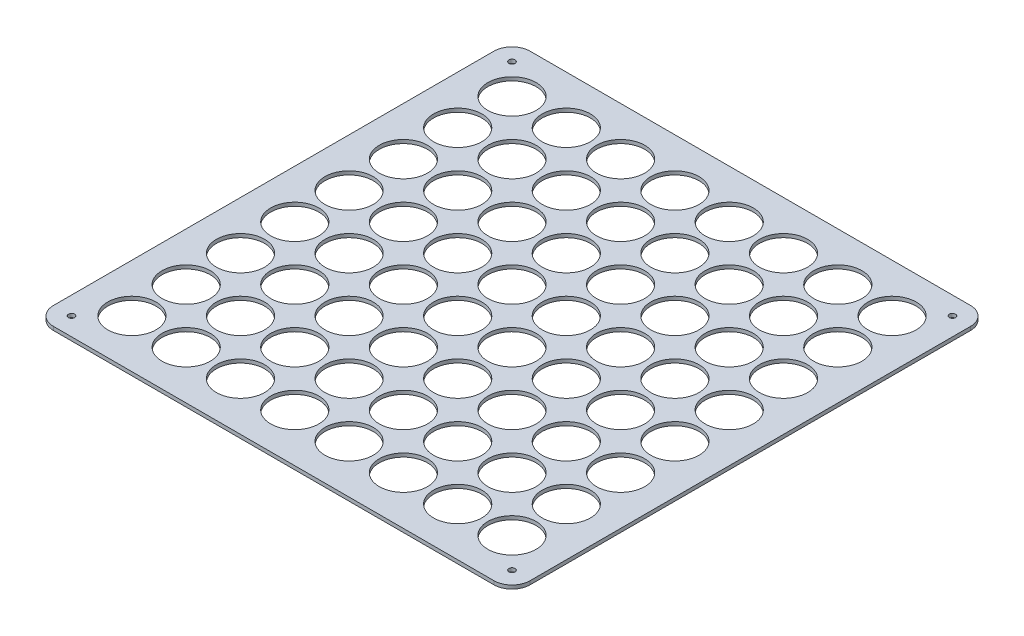
SolidWorks part; units mm, degrees
ref_plane "Front Plane" through (0, 0, 0) normal (0, 0, 1) x (1, 0, 0)
ref_plane "Top Plane" through (0, 0, 0) normal (0, 1, 0) x (1, 0, 0)
ref_plane "Right Plane" through (0, 0, 0) normal (1, 0, 0) x (0, 0, -1)
sketch "Sketch1" plane through (0, 0, 0) normal (0, 1, 0) x (1, 0, 0)
  line L1 (-197.5, 197.5) -> (197.5, 197.5)
  line L2 (-197.5, 197.5) -> (-197.5, -197.5)
  line L3 (-197.5, -197.5) -> (197.5, -197.5)
  line L4 (197.5, 197.5) -> (197.5, -197.5)
  line L5 (-197.5, 197.5) -> (197.5, -197.5) construction
  line L6 (-197.5, -197.5) -> (197.5, 197.5) construction
  circle A0 centre (-182.5, 182.5) radius 2.55
  circle A1 centre (182.5, 182.5) radius 2.55
  circle A2 centre (182.5, -182.5) radius 2.55
  circle A3 centre (-182.5, -182.5) radius 2.55
  point P0 (0, 0)
  dimension "D4" = 5.1
  dimension "D6" = 5.1
  dimension "D8" = 5.1
  dimension "D10" = 5.1
  dimension "D1" = 395
  dimension "D2" = 395
  dimension "D3" = 15
  dimension "D5" = 15
  dimension "D7" = 15
  dimension "D9" = 15
extrude "Boss-Extrude1" add sketch "Sketch1" along normal blind 3
fillet "Fillet1" radius 15 4 edges at (-197.5, 1.5, -197.5) (197.5, 1.5, -197.5) (197.5, 1.5, 197.5) (-197.5, 1.5, 197.5)
sketch "Sketch2" plane through (0, 3, 0) normal (0, 1, 0) x (1, 0, 0)
  line L0 (-182.5, -197.5) -> (182.5, -197.5) construction
  line L1 (-197.5, 182.5) -> (-197.5, -182.5) construction
  circle A0 centre (-157.5, -157.5) radius 20
  dimension "D1" = 40
  dimension "D2" = 40
  dimension "D3" = 40
extrude "Cut-Extrude1" cut sketch "Sketch2" against normal through all
pattern_linear "LPattern1" count 8 spacing 45 along (0, 0, -1) count 8 spacing 45 along (1, 0, 0) of "Cut-Extrude1"
